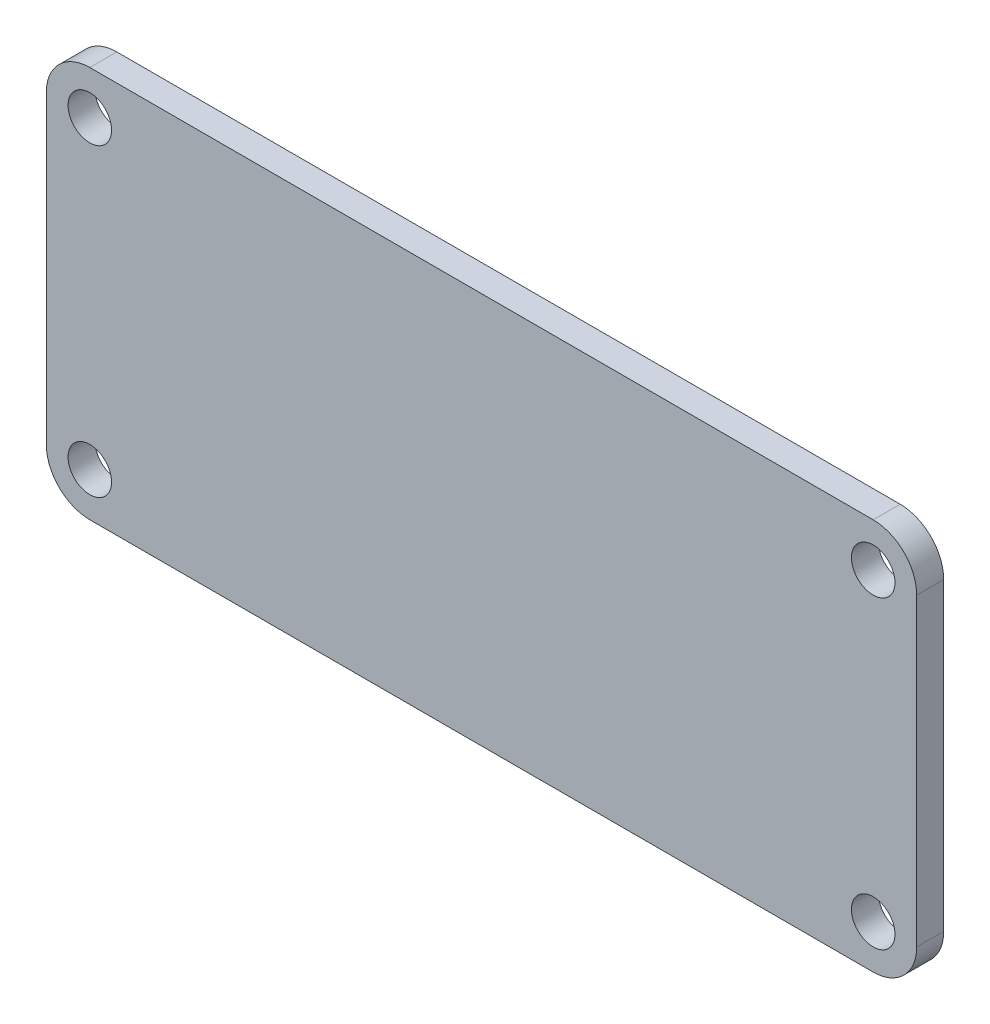
SolidWorks part; units mm, degrees
ref_plane "Front Plane" through (0, 0, 0) normal (0, 0, 1) x (1, 0, 0)
ref_plane "Top Plane" through (0, 0, 0) normal (0, 1, 0) x (1, 0, 0)
ref_plane "Right Plane" through (0, 0, 0) normal (1, 0, 0) x (0, 0, -1)
sketch "Sketch1" plane through (0, 0, 0) normal (0, 0, 1) x (1, 0, 0)
  line L1 (25.4, -11.43) -> (-25.4, -11.43)
  line L2 (25.4, -11.43) -> (25.4, 11.43)
  line L3 (25.4, 11.43) -> (-25.4, 11.43)
  line L4 (-25.4, -11.43) -> (-25.4, 11.43)
  line L5 (25.4, -11.43) -> (-25.4, 11.43) construction
  line L6 (25.4, 11.43) -> (-25.4, -11.43) construction
  point P0 (0, 0)
  dimension "D1" = 22.86
  dimension "D2" = 50.8
extrude "Boss-Extrude1" add sketch "Sketch1" along normal blind 1.5748
sketch "Sketch2" plane through (0, 0, 1.5748) normal (0, 0, 1) x (1, 0, 0)
  line L0 (-25.4, 11.43) -> (-25.4, -11.43) construction
  line L1 (25.4, 11.43) -> (-25.4, 11.43) construction
  line L2 (25.4, -11.43) -> (25.4, 11.43) construction
  line L3 (-25.4, -11.43) -> (25.4, -11.43) construction
  circle A0 centre (-22.86, 8.89) radius 1.27
  circle A1 centre (22.86, 8.89) radius 1.27
  circle A2 centre (-22.86, -8.89) radius 1.27
  circle A3 centre (22.86, -8.89) radius 1.27
  point P8 (23.4019, -9.2154)
  dimension "D1" = 2.54
  dimension "D2" = 1.27
  dimension "D3" = 1.27
  dimension "D4" = 1.27
  dimension "D5" = 1.27
extrude "Cut-Extrude1" cut sketch "Sketch2" against normal through all
fillet "Fillet1" radius 2.54 4 edges at (25.4, 11.43, 0.7874) (25.4, -11.43, 0.7874) (-25.4, -11.43, 0.7874) (-25.4, 11.43, 0.7874)
